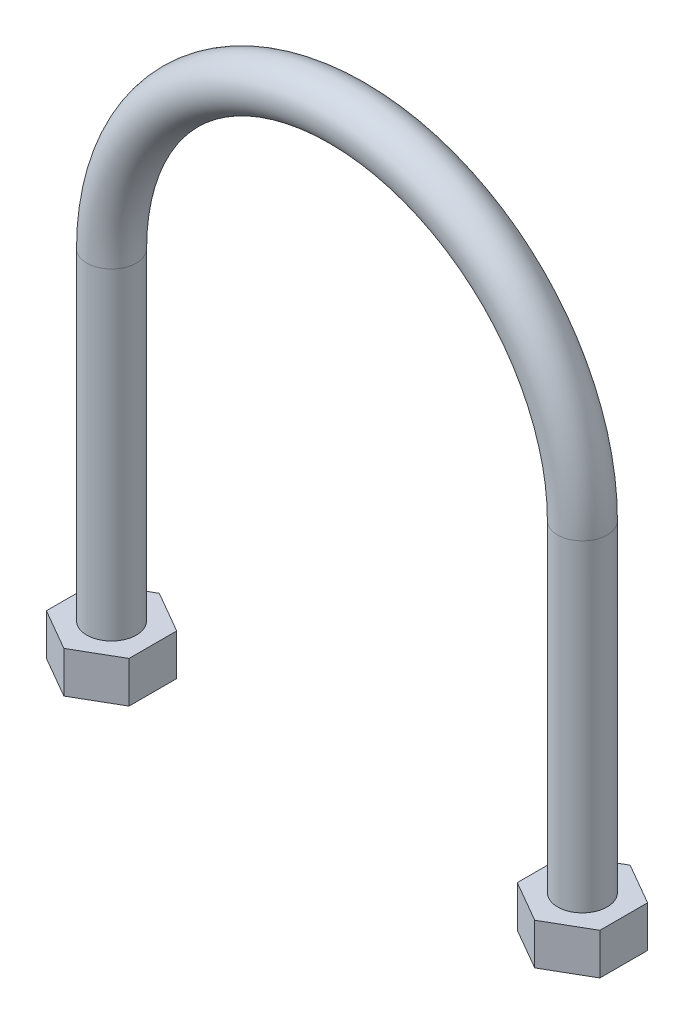
SolidWorks part; units mm, degrees
material "AISI 304"
ref_plane "Front Plane" through (0, 0, 0) normal (0, 0, 1) x (1, 0, 0)
ref_plane "Top Plane" through (0, 0, 0) normal (0, 1, 0) x (1, 0, 0)
ref_plane "Right Plane" through (0, 0, 0) normal (1, 0, 0) x (0, 0, -1)
sketch "Sketch1" plane through (0, 0, 0) normal (0, 0, 1) x (1, 0, 0)
  line L0 (-28.5, 0) -> (-28.5, -42.5)
  line L1 (28.5, 0) -> (28.5, -42.5)
  line L2 (0, 28.5) -> (-35.385, 28.5) construction
  arc A0 (28.5, 0) -> (-28.5, 0) centre (0, 0) ccw
  dimension "D1" = 57
  dimension "D2" = 71
sweep "Sweep1" add path "Sketch1" circular profile diameter 6 parameters "D3"=6
ref_plane "Plane1" through (0, -39, 0) normal (0, 1, 0) x (1, 0, 0)
sketch "Sketch14" plane through (0, -39, 0) normal (0, 1, 0) x (1, 0, 0)
  line L0 (0, 0) -> (0, 14.4355) construction
  line L1 (-28.5, 5.7735) -> (-33.5, 2.8868)
  line L2 (-33.5, 2.8868) -> (-33.5, -2.8868)
  line L3 (-33.5, -2.8868) -> (-28.5, -5.7735)
  line L4 (-28.5, -5.7735) -> (-23.5, -2.8868)
  line L5 (-23.5, -2.8868) -> (-23.5, 2.8868)
  line L6 (-23.5, 2.8868) -> (-28.5, 5.7735)
  line L7 (23.5, 2.8868) -> (28.5, 5.7735)
  line L8 (23.5, -2.8868) -> (23.5, 2.8868)
  line L9 (28.5, -5.7735) -> (23.5, -2.8868)
  line L10 (33.5, -2.8868) -> (28.5, -5.7735)
  line L11 (33.5, 2.8868) -> (33.5, -2.8868)
  line L12 (28.5, 5.7735) -> (33.5, 2.8868)
  circle A0 centre (-28.5, 0) radius 5 construction
  dimension "D1" = 10
extrude "Boss-Extrude1" add sketch "Sketch14" against normal blind 5
